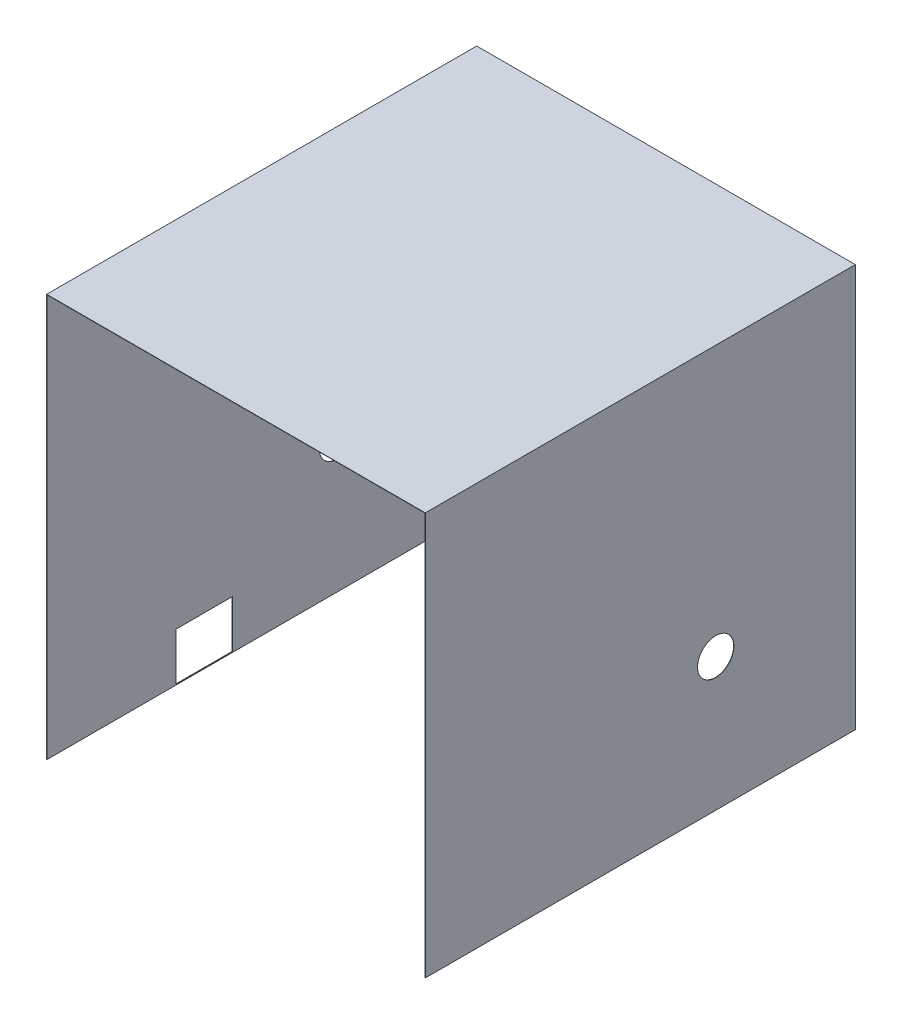
SolidWorks part; units mm, degrees
ref_plane "Front Plane" through (0, 0, 0) normal (0, 0, 1) x (1, 0, 0)
ref_plane "Top Plane" through (0, 0, 0) normal (0, 1, 0) x (1, 0, 0)
ref_plane "Right Plane" through (0, 0, 0) normal (1, 0, 0) x (0, 0, -1)
sketch "Sketch1" plane through (0, 0, 0) normal (0, 0, 1) x (1, 0, 0)
  line L0 (-344.518, 0) -> (-344.518, 499.3)
  line L2 (124.782, 499.3) -> (124.782, 0)
  line L3 (-344.518, 0) -> (-344.168, 0)
  line L4 (-344.168, 0) -> (-344.168, 498.95)
  line L6 (124.432, 498.95) -> (124.432, 0)
  line L7 (124.432, 0) -> (124.782, 0)
  line L8 (-344.518, 499.3) -> (124.782, 499.3)
  line L9 (-344.168, 498.95) -> (124.432, 498.95)
  dimension "D1" = 499.3
  dimension "D2" = 0.35
  dimension "D3" = 469.3
  dimension "D4" = 0.35
  dimension "D5" = 0.35
extrude "Boss-Extrude1" add sketch "Sketch1" along normal blind 533
sketch "Sketch2" plane through (124.782, 0, 0) normal (1, 0, 0) x (0, 0, -1)
  line L2 (-533, 0) -> (-533, 499.3) construction
  line L3 (-533, 0) -> (0, 0) construction
  circle A0 centre (-173, 165) radius 22.5
  dimension "D1" = 360
  dimension "D2" = 165
  dimension "D3" = 45
extrude "Cut-Extrude1" cut sketch "Sketch2" against normal blind 533
sketch "Sketch3" plane through (-344.518, 0, 0) normal (-1, 0, 0) x (0, 0, 1)
  line L0 (303, 1) -> (373, 1)
  line L1 (373, 1) -> (373, 60)
  line L2 (373, 60) -> (303, 60)
  line L3 (303, 60) -> (303, 1)
  line L5 (533, 0) -> (0, 0) construction
  line L6 (533, 499.3) -> (533, 0) construction
  dimension "D1" = 70
  dimension "D2" = 59
  dimension "D3" = 1
  dimension "D4" = 160
extrude "Cut-Extrude2" cut sketch "Sketch3" against normal blind 243
